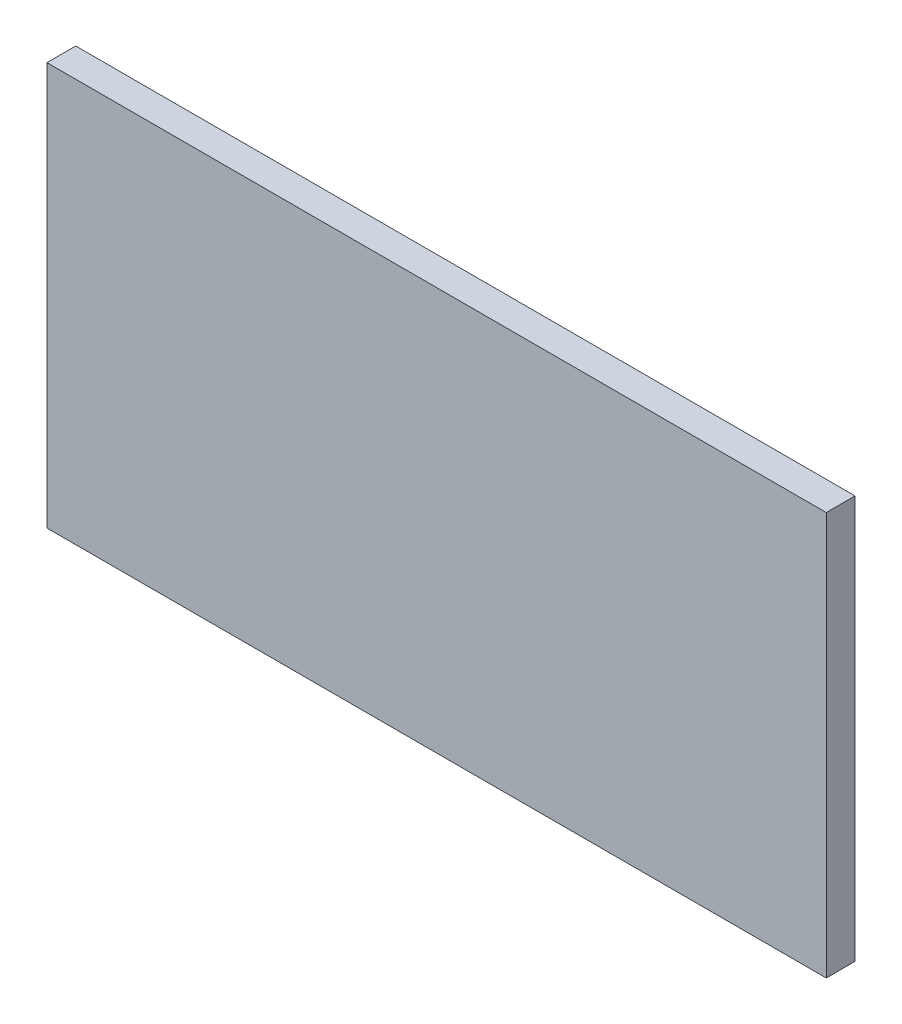
SolidWorks part; units mm, degrees
ref_plane "Front" through (0, 0, 0) normal (0, 0, 1) x (1, 0, 0)
ref_plane "Top" through (0, 0, 0) normal (0, 1, 0) x (1, 0, 0)
ref_plane "Right" through (0, 0, 0) normal (1, 0, 0) x (0, 0, -1)
sketch "Sketch1" plane through (0, 0, 0) normal (0, 0, 1) x (1, 0, 0)
  line L1 (0, 0) -> (40.6, 0)
  line L2 (0, 0) -> (0, 21)
  line L3 (0, 21) -> (40.6, 21)
  line L4 (40.6, 0) -> (40.6, 21)
  dimension "D1" = 21
  dimension "D2" = 40.6
extrude "Boss-Extrude1" add sketch "Sketch1" along normal blind 1.5 contours L3 L4 L1 L2
sketch "Sketch2" plane through (0, 0, 0) normal (0, 0, -1) x (-1, 0, 0)
  line L1 (-6.5, 11.81) -> (-10.26, 11.81)
  line L2 (-6.5, 11.81) -> (-6.5, 14.81)
  line L3 (-6.5, 14.81) -> (-10.26, 14.81)
  line L4 (-10.26, 11.81) -> (-10.26, 14.81)
  line L5 (0, 0) -> (0, 21) construction
  line L6 (0, 21) -> (-40.6, 21) construction
  dimension "D1" = 6.5
  dimension "3.7" = 3.76
  dimension "D3" = 3
  dimension "D4" = 6.19
extrude "Boss-Extrude3" add sketch "Sketch2" along normal blind 1.1
sketch "Sketch3" plane through (0, 0, -1.1) normal (0, 0, -1) x (-1, 0, 0)
  line L0 (-10.26, 13.31) -> (-6.5, 13.31) construction
  line L1 (-10.26, 14.81) -> (-10.26, 11.81) construction
  line L2 (-6.5, 11.81) -> (-6.5, 14.81) construction
  line L3 (-10.26, 11.81) -> (-6.5, 11.81) construction
  circle A0 centre (-9.08, 13.31) radius 0.25
  dimension "D1" = 1.5
  dimension "D3" = 0.5
  dimension "D2" = 1.18
extrude "Cut-Extrude1" cut sketch "Sketch3" against normal blind 0.5 contours A0
fillet "Fillet3" radius 0.5 4 edges at (10.26, 13.31, -1.1) (8.38, 14.81, -1.1) (6.5, 13.31, -1.1) (8.38, 11.81, -1.1)
sketch "Sketch4" plane through (0, 0, 0) normal (0, 0, -1) x (-1, 0, 0)
  line L0 (0, 0) -> (0, 21) construction
  line L1 (0, 21) -> (-40.6, 21) construction
  circle A0 centre (-18.925, 3.72) radius 0.65
  circle A1 centre (-20.675, 3.72) radius 0.65
  circle A2 centre (-20.675, 5.47) radius 0.65
  circle A3 centre (-20.675, 7.22) radius 0.65
  circle A4 centre (-18.925, 5.47) radius 0.65
  circle A5 centre (-18.925, 7.22) radius 0.65
  dimension "D1" = 18.925
  dimension "D4" = 1.3
  dimension "D5" = 17.28
  dimension "D2" = 2
  dimension "D3" = 3
extrude "Boss-Extrude4" add sketch "Sketch4" along normal blind 0.25
